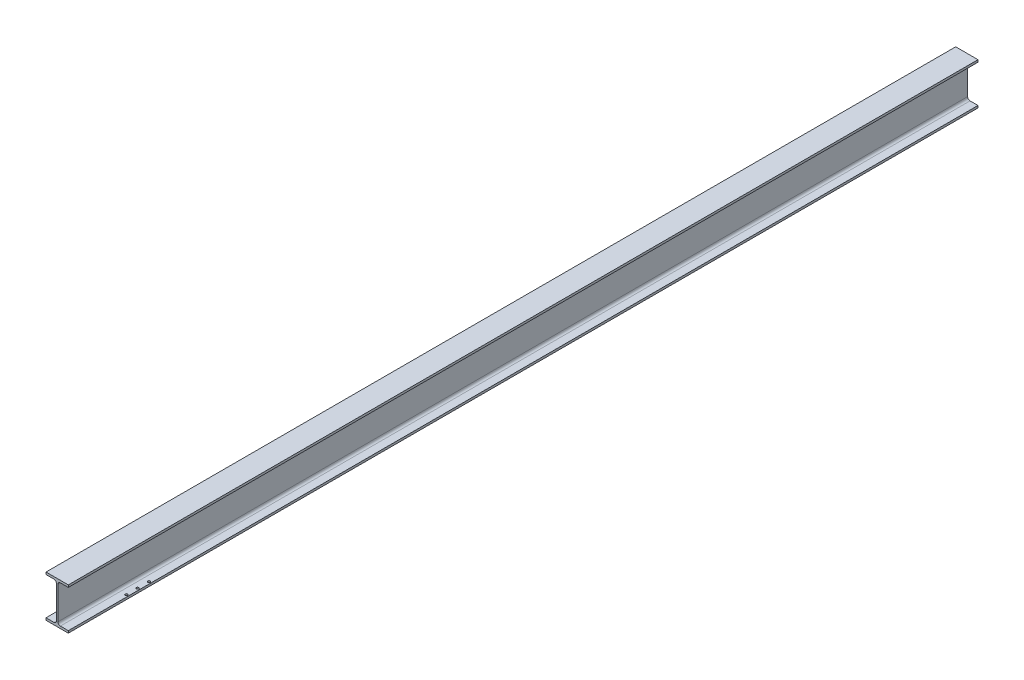
SolidWorks part; units mm, degrees
ref_plane "Front Plane" through (0, 0, 0) normal (0, 0, 1) x (1, 0, 0)
ref_plane "Top Plane" through (0, 0, 0) normal (0, 1, 0) x (1, 0, 0)
ref_plane "Right Plane" through (0, 0, 0) normal (1, 0, 0) x (0, 0, -1)
sketch "Sketch1" plane through (0, 0, 0) normal (0, 0, 1) x (1, 0, 0)
  line L0 (0, 60) -> (0, -60)
  line L1 (0, -60) -> (-32, -60)
  line L2 (-32, -60) -> (-32, -53.7)
  line L3 (-32, -53.7) -> (-2.2, -53.7)
  line L4 (-2.2, -53.7) -> (-2.2, 53.7)
  line L5 (-2.2, 53.7) -> (-32, 53.7)
  line L6 (-32, 53.7) -> (-32, 60)
  line L7 (-32, 60) -> (0, 60)
  dimension "D1" = 120
  dimension "D2" = 60
  dimension "D3" = 32
  dimension "D4" = 0
  dimension "D5" = 6.3
  dimension "D6" = 6.3
  dimension "D7" = 2.2
extrude "Boss-Extrude1" add sketch "Sketch1" along normal mid plane 2610
mirror "Mirror1" about plane through (0, 60, 1305) normal (-1, 0, 0) of "Boss-Extrude1"
sketch "Sketch2" plane through (0, -60, 0) normal (0, -1, 0) x (1, 0, 0)
  line L0 (-32, 1305) -> (32, 1305) construction
  line L1 (26, 1303.4786) -> (26, 926.9453) construction
  point P4 (26, 1280)
  point P5 (26, 1258)
  point P6 (26, 1236)
  point P7 (26, 1214)
  point P8 (26, 1126)
  point P9 (26, 1104)
  point P10 (26, 1082)
  point P11 (26, 1060)
  dimension "D1" = 26
  dimension "D2" = 25
  dimension "D3" = 47
  dimension "D4" = 69
  dimension "D5" = 91
  dimension "D6" = 179
  dimension "D7" = 201
  dimension "D8" = 223
  dimension "D9" = 245
fillet "Fillet1" radius 7 4 edges at (2.2, -53.7, 0) (2.2, 53.7, 0) (-2.2, 53.7, 0) (-2.2, -53.7, 0)
sketch "Sketch3" plane through (0, -60, 0) normal (0, -1, 0) x (1, 0, 0)
  line L0 (-32, 1305) -> (32, 1305) construction
  point P0 (26, 1132.5)
  dimension "D1" = 172.5
  dimension "D2" = 26
hole_wizard "Ø7.0 (7) Diameter Hole1" positions "Sketch4" profile "Sketch5" hole size "Ø7.0" standard "ISO" end condition up to next
sketch "Sketch4" plane through (0, -60, 0) normal (0, -1, 0) x (-1, 0, 0)
  point P0 (-26, -1132.5)
sketch "Sketch5" plane through (26, -60, 1132.5) normal (1, 0, 0) x (0, 0, -1)
  line L0 (0, 0) -> (0, 6.3)
  line L1 (0, 6.3) -> (3.5, 6.3)
  line L2 (3.5, 6.3) -> (3.5, 0)
  line L5 (3.5, 0) -> (0, 0)
  line L11 (0, -6.35) -> (0, 107.95) construction
  dimension "Thru Hole Dia." = 7
  dimension "Thru Hole Depth" = 6.3
pattern_linear "LPattern1" count 3 spacing 32.5 along (0, 0, -1) count 2 spacing 52 along (-1, 0, 0) of "Ø7.0 (7) Diameter Hole1"
